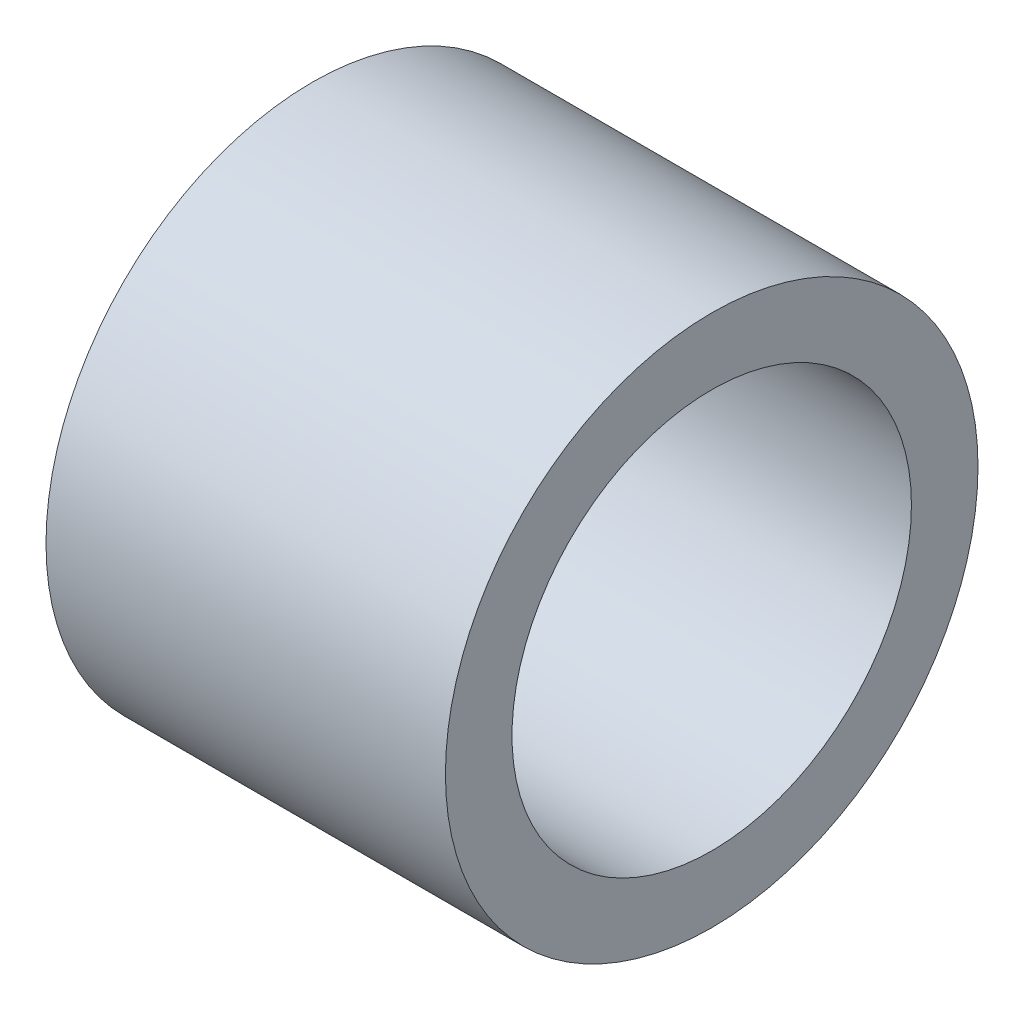
SolidWorks part; units mm, degrees
ref_plane "Plan de face" through (0, 0, 0) normal (0, 0, 1) x (1, 0, 0)
ref_plane "Plan de dessus" through (0, 0, 0) normal (0, 1, 0) x (1, 0, 0)
ref_plane "Plan de droite" through (0, 0, 0) normal (1, 0, 0) x (0, 0, -1)
sketch "Esquisse1" plane through (0, 0, 0) normal (1, 0, 0) x (0, 0, -1)
  circle A0 centre (0, 0) radius 9.525
  circle A1 centre (0, 0) radius 12.7
  dimension "D1" = 19.05
  dimension "D2" = 25.4
extrude "Boss.-Extru.1" add sketch "Esquisse1" along normal mid plane 19.05
